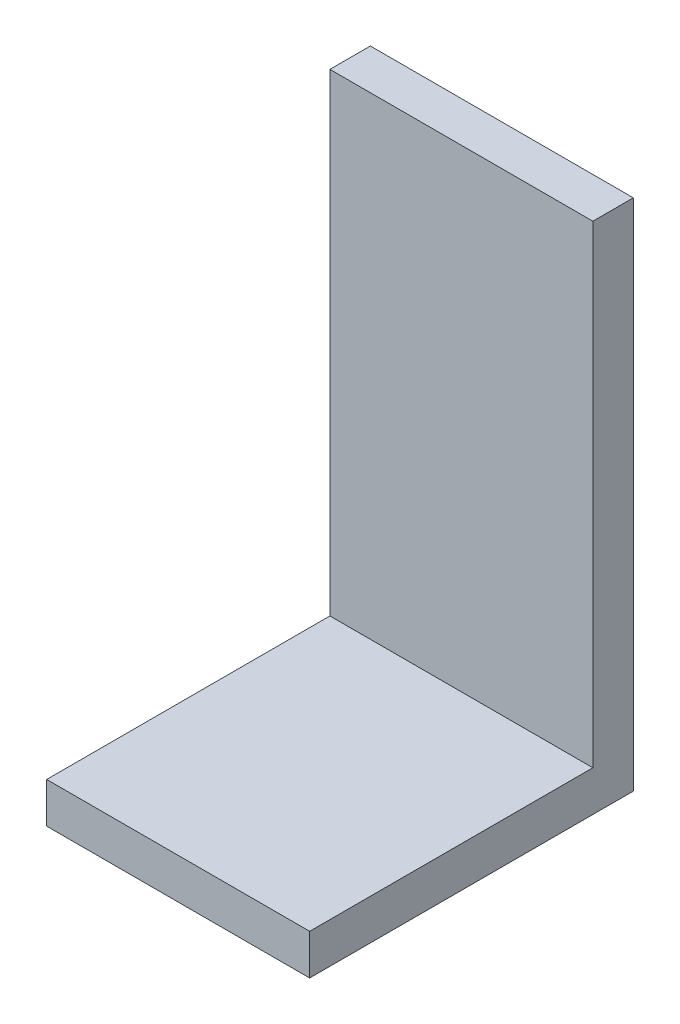
SolidWorks part; units mm, degrees
ref_plane "Front Plane" through (0, 0, 0) normal (0, 0, 1) x (1, 0, 0)
ref_plane "Top Plane" through (0, 0, 0) normal (0, 1, 0) x (1, 0, 0)
ref_plane "Right Plane" through (0, 0, 0) normal (1, 0, 0) x (0, 0, -1)
sketch "Sketch1" plane through (0, 0, 0) normal (0, 1, 0) x (1, 0, 0)
  line L1 (-47.6444, 37.6889) -> (-34.6444, 37.6889)
  line L2 (-47.6444, 37.6889) -> (-47.6444, 21.6889)
  line L3 (-47.6444, 21.6889) -> (-34.6444, 21.6889)
  line L4 (-34.6444, 37.6889) -> (-34.6444, 21.6889)
  dimension "D1" = 16
  dimension "D2" = 13
extrude "Boss-Extrude1" add sketch "Sketch1" along normal blind 2
sketch "Sketch2" plane through (0, 2, 0) normal (0, 1, 0) x (1, 0, 0)
  line L0 (-34.6444, 21.6889) -> (-34.6444, 37.6889) construction
  line L1 (-47.6444, 37.6889) -> (-34.6444, 37.6889)
  line L2 (-47.6444, 37.6889) -> (-47.6444, 35.6889)
  line L3 (-47.6444, 35.6889) -> (-34.6444, 35.6889)
  line L4 (-34.6444, 37.6889) -> (-34.6444, 35.6889)
  dimension "D1" = 2
extrude "Boss-Extrude2" add sketch "Sketch2" along normal blind 23.4
